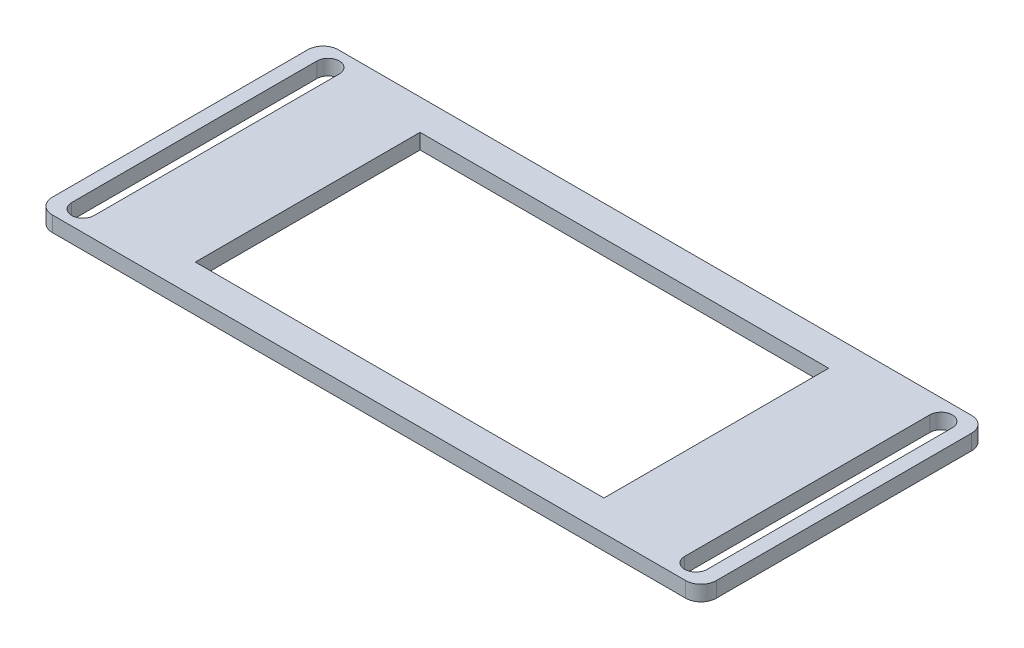
SolidWorks part; units mm, degrees
ref_plane "Front" through (0, 0, 0) normal (0, 0, 1) x (1, 0, 0)
ref_plane "Top" through (0, 0, 0) normal (0, 1, 0) x (1, 0, 0)
ref_plane "Right" through (0, 0, 0) normal (1, 0, 0) x (0, 0, -1)
sketch "Sketch1" plane through (0, 0, 0) normal (0, 1, 0) x (1, 0, 0)
  line L1 (-32.5, -14) -> (32.5, -14)
  line L2 (-32.5, -14) -> (-32.5, 14)
  line L3 (-32.5, 14) -> (32.5, 14)
  line L4 (32.5, -14) -> (32.5, 14)
  line L5 (-32.5, -14) -> (32.5, 14) construction
  line L6 (-32.5, 14) -> (32.5, -14) construction
  line L7 (-20, -11) -> (20, -11)
  line L8 (-20, -11) -> (-20, 11)
  line L9 (-20, 11) -> (20, 11)
  line L10 (20, -11) -> (20, 11)
  line L11 (-20, -11) -> (20, 11) construction
  line L12 (-20, 11) -> (20, -11) construction
  point P0 (0, 0)
  point P5 (0, 0)
  dimension "D1" = 28
  dimension "D2" = 65
  dimension "D3" = 40
  dimension "D4" = 3
extrude "Boss-Extrude1" add sketch "Sketch1" along normal blind 1.5
sketch "Sketch2" plane through (0, 1.5, 0) normal (0, 1, 0) x (1, 0, 0)
  line L0 (-30, -12) -> (-30, 12) construction
  line L1 (-31.1, -12) -> (-31.1, 12)
  line L2 (-28.9, -12) -> (-28.9, 12)
  line L3 (0, 0) -> (-30, 0) construction
  line L4 (0, 0) -> (0, 14) construction
  line L5 (32.5, 14) -> (-32.5, 14) construction
  line L6 (30, -12) -> (30, 12) construction
  line L7 (31.1, -12) -> (31.1, 12)
  line L8 (28.9, -12) -> (28.9, 12)
  line L9 (-32.5, -14) -> (32.5, -14) construction
  arc A0 (-31.1, -12) -> (-28.9, -12) centre (-30, -12) ccw
  arc A1 (-28.9, 12) -> (-31.1, 12) centre (-30, 12) ccw
  arc A2 (31.1, -12) -> (28.9, -12) centre (30, -12) cw
  arc A3 (28.9, 12) -> (31.1, 12) centre (30, 12) cw
  point P2 (-30, 0)
  point P15 (30, 0)
  dimension "D3" = 2.2
  dimension "D1" = 60
  dimension "D2" = 2
extrude "Cut-Extrude1" cut sketch "Sketch2" against normal through all
fillet "Fillet2" radius 1.5 4 edges at (-32.5, 0.75, -14) (32.5, 0.75, -14) (32.5, 0.75, 14) (-32.5, 0.75, 14)
